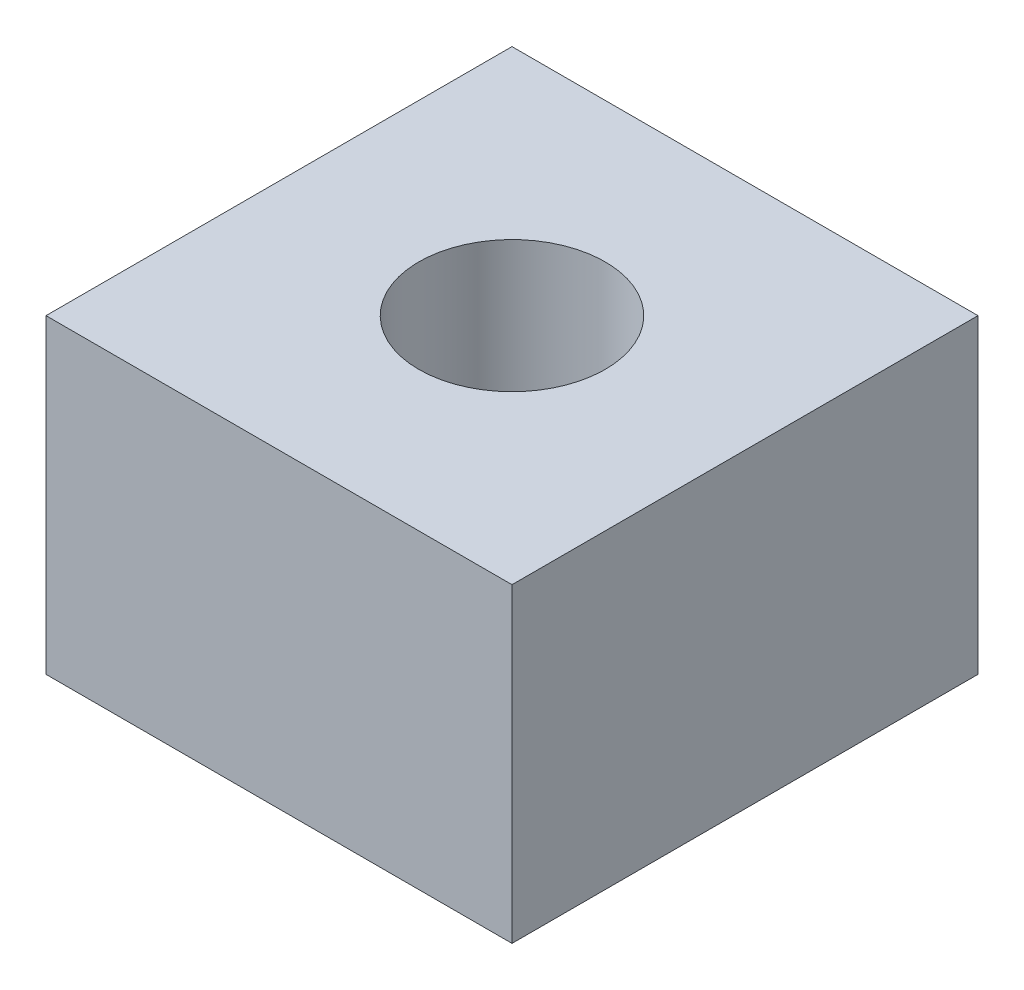
SolidWorks part; units mm, degrees
ref_plane "Front Plane" through (0, 0, 0) normal (0, 0, 1) x (1, 0, 0)
ref_plane "Top Plane" through (0, 0, 0) normal (0, 1, 0) x (1, 0, 0)
ref_plane "Right Plane" through (0, 0, 0) normal (1, 0, 0) x (0, 0, -1)
sketch "Sketch1" plane through (0, 0, 0) normal (0, 0, 1) x (1, 0, 0)
  line L1 (-19.7814, -7.7753) -> (10.2186, -7.7753)
  line L2 (-19.7814, -7.7753) -> (-19.7814, -27.7753)
  line L3 (-19.7814, -27.7753) -> (10.2186, -27.7753)
  line L4 (10.2186, -7.7753) -> (10.2186, -27.7753)
extrude "Boss-Extrude1" add sketch "Sketch1" along normal blind 30
sketch "Sketch3" plane through (0, -7.7753, 0) normal (0, 1, 0) x (1, 0, 0)
  circle A0 centre (-4.7814, -15) radius 6
extrude "Cut-Extrude1" cut sketch "Sketch3" against normal through all
